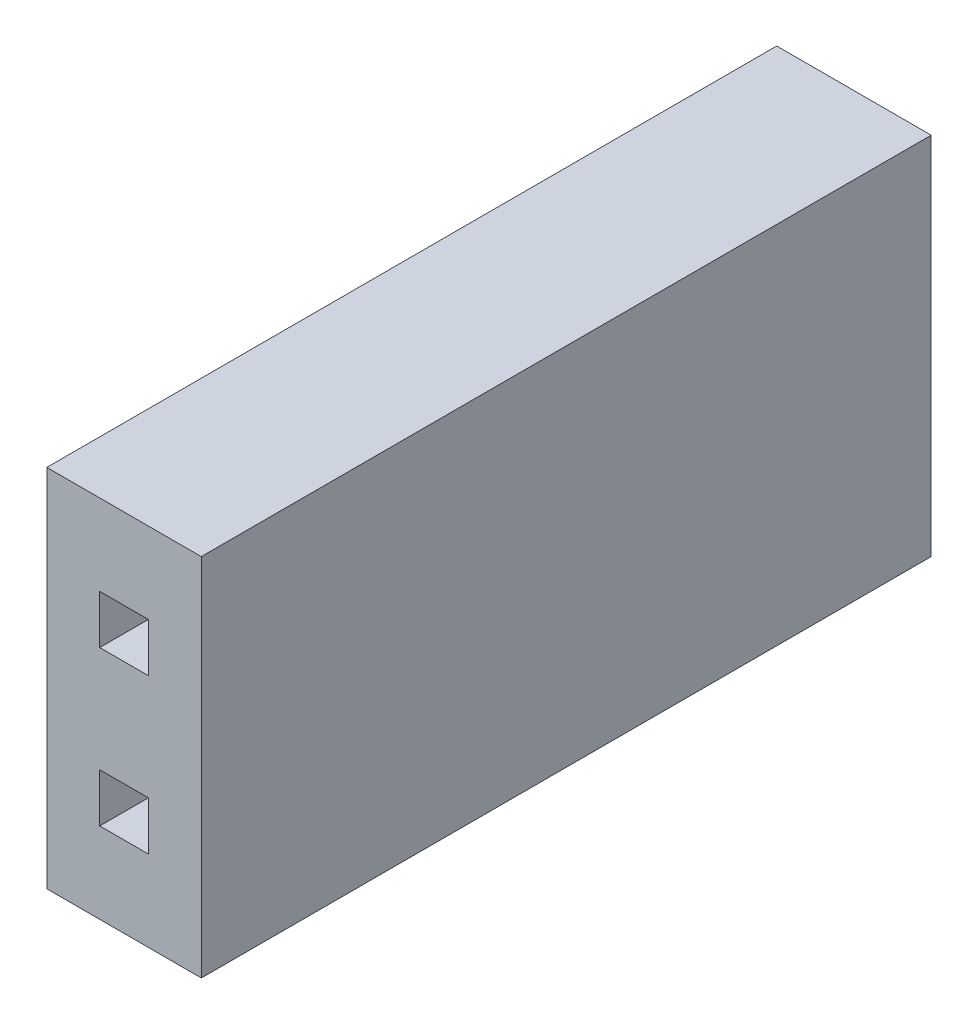
SolidWorks part; units mm, degrees
material "ПВХ Жесткий"
ref_plane "Спереди" through (0, 0, 0) normal (0, 0, 1) x (1, 0, 0)
ref_plane "Сверху" through (0, 0, 0) normal (0, 1, 0) x (1, 0, 0)
ref_plane "Справа" through (0, 0, 0) normal (1, 0, 0) x (0, 0, -1)
other "Configuration Table"
sketch "Эскиз1" plane through (0, 0, 0) normal (0, 0, 1) x (1, 0, 0)
  line L1 (0, 0) -> (2.54, 0)
  line L2 (0, 0) -> (0, 6)
  line L3 (0, 6) -> (2.54, 6)
  line L4 (2.54, 0) -> (2.54, 6)
  dimension "D1" = 6
  dimension "D2" = 2.54
extrude "Бобышка-Вытянуть1" add sketch "Эскиз1" along normal blind 12
sketch "Эскиз2" plane through (0, 0, 0) normal (0, 0, -1) x (-1, 0, 0)
  line L0 (0, 0) -> (-2.54, 0) construction
  line L5 (-2.27, 5.27) -> (-0.27, 5.27)
  line L6 (-2.27, 5.27) -> (-2.27, 3.27)
  line L7 (-2.27, 3.27) -> (-0.27, 3.27)
  line L8 (-0.27, 5.27) -> (-0.27, 3.27)
  line L9 (-2.27, 5.27) -> (-0.27, 3.27) construction
  line L10 (-2.27, 3.27) -> (-0.27, 5.27) construction
  line L11 (-2.27, 2.73) -> (-0.27, 2.73)
  line L12 (-2.27, 2.73) -> (-2.27, 0.73)
  line L13 (-2.27, 0.73) -> (-0.27, 0.73)
  line L14 (-0.27, 2.73) -> (-0.27, 0.73)
  line L15 (-2.27, 2.73) -> (-0.27, 0.73) construction
  line L16 (-2.27, 0.73) -> (-0.27, 2.73) construction
  point P0 (-1.27, 4.27)
  point P5 (-1.27, 1.73)
  point P10 (0, 0)
  point P12 (-1.27, 0)
  dimension "D1" = 2
  dimension "D2" = 2.54
  dimension "D3" = 1.73
extrude "Вырез-Вытянуть1" cut sketch "Эскиз2" against normal blind 4
sketch "Эскиз3" plane through (0, 0, 4) normal (0, 0, -1) x (-1, 0, 0)
  line L0 (-2.27, 5.27) -> (-2.27, 3.27) construction
  line L1 (-2.27, 2.73) -> (-2.27, 0.73) construction
  line L2 (-0.27, 2.73) -> (-2.27, 2.73) construction
  circle A0 centre (-1.27, 4.27) radius 0.65
  circle A1 centre (-1.27, 1.73) radius 0.65
  point P0 (-1.27, 4.27)
  point P1 (-1.27, 1.73)
  point P2 (-2.27, 4.27)
  point P3 (-2.27, 1.73)
  point P6 (-1.27, 2.73)
  dimension "D1" = 1.3
extrude "Бобышка-Вытянуть2" add sketch "Эскиз3" along normal up to surface (4 mm away) up to face at (1.27, 4.27, 0)
sketch "Эскиз4" plane through (0, 0, 12) normal (0, 0, 1) x (1, 0, 0)
  line L1 (0.87, 3.87) -> (1.67, 3.87)
  line L2 (0.87, 3.87) -> (0.87, 4.67)
  line L3 (0.87, 4.67) -> (1.67, 4.67)
  line L4 (1.67, 3.87) -> (1.67, 4.67)
  line L5 (0.87, 3.87) -> (1.67, 4.67) construction
  line L6 (0.87, 4.67) -> (1.67, 3.87) construction
  line L7 (0.87, 1.33) -> (1.67, 1.33)
  line L8 (0.87, 1.33) -> (0.87, 2.13)
  line L9 (0.87, 2.13) -> (1.67, 2.13)
  line L10 (1.67, 1.33) -> (1.67, 2.13)
  line L11 (0.87, 1.33) -> (1.67, 2.13) construction
  line L12 (0.87, 2.13) -> (1.67, 1.33) construction
  point P0 (1.27, 4.27)
  point P1 (1.27, 1.73)
  point P3 (1.27, 4.27)
  point P9 (1.27, 1.73)
  dimension "D1" = 0.8
extrude "Вырез-Вытянуть2" cut sketch "Эскиз4" against normal blind 5
